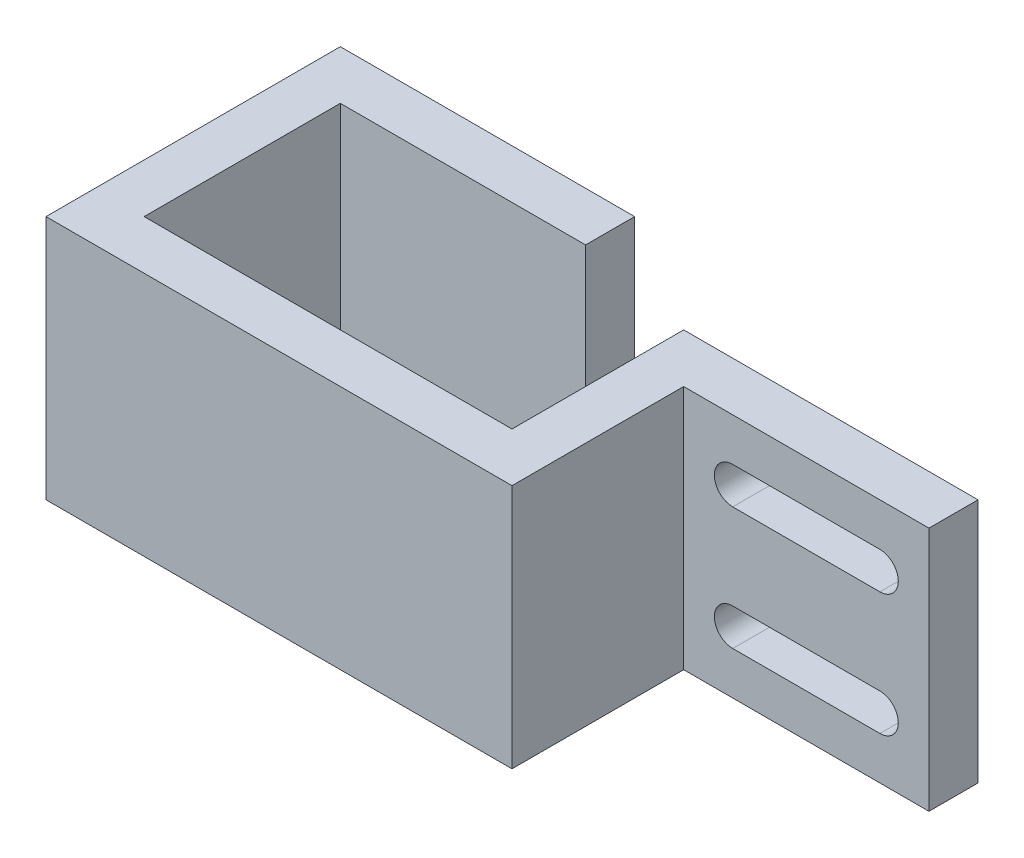
SolidWorks part; units mm, degrees
ref_plane "Front Plane" through (0, 0, 0) normal (0, 0, 1) x (1, 0, 0)
ref_plane "Top Plane" through (0, 0, 0) normal (0, 1, 0) x (1, 0, 0)
ref_plane "Right Plane" through (0, 0, 0) normal (1, 0, 0) x (0, 0, -1)
sketch "Croquis1" plane through (0, 0, 0) normal (0, 1, 0) x (1, 0, 0)
  line L0 (-19, 24) -> (-15, 24)
  line L1 (-15, 24) -> (-15, 4)
  line L2 (-15, 4) -> (15, 4)
  line L3 (15, 4) -> (15, 18)
  line L4 (15, 18) -> (39, 18)
  line L5 (39, 18) -> (39, 14)
  line L6 (39, 14) -> (19, 14)
  line L7 (19, 14) -> (19, 0)
  line L8 (19, 0) -> (-19, 0)
  line L9 (-19, 0) -> (-19, 24)
  point P2 (0, 0)
  dimension "D1" = 38
  dimension "D2" = 4
  dimension "D3" = 4
  dimension "D4" = 4
  dimension "D5" = 24
  dimension "D6" = 18
  dimension "D7" = 4
  dimension "D8" = 24
extrude "Saliente-Extruir1" add sketch "Croquis1" along normal blind 20
sketch "Croquis2" plane through (0, 0, -14) normal (0, 0, 1) x (1, 0, 0)
  line L0 (39, 10) -> (19, 10) construction
  line L1 (39, 20) -> (39, 0) construction
  line L2 (29, 20) -> (29, 10) construction
  line L3 (19, 20) -> (39, 20) construction
  line L4 (29, 15) -> (39, 15) construction
  line L5 (19, 20) -> (19, 0) construction
  line L6 (35, 16.5) -> (23, 16.5)
  line L7 (35, 13.5) -> (23, 13.5)
  line L8 (35, 3.5) -> (23, 3.5)
  line L9 (35, 6.5) -> (23, 6.5)
  arc A0 (35, 13.5) -> (35, 16.5) centre (35, 15) ccw
  arc A1 (23, 13.5) -> (23, 16.5) centre (23, 15) cw
  arc A2 (35, 6.5) -> (35, 3.5) centre (35, 5) cw
  arc A3 (23, 6.5) -> (23, 3.5) centre (23, 5) ccw
  point P15 (29, 13.5)
  point P20 (29, 16.5)
  dimension "D1" = 3
  dimension "D2" = 6
extrude "Cortar-Extruir1" cut sketch "Croquis2" against normal blind 20
sketch "Croquis3" plane through (-15, 0, 0) normal (1, 0, 0) x (0, 0, -1)
  line L0 (24, 20) -> (20, 20)
  line L1 (4, 20) -> (24, 20) construction
  line L2 (20, 20) -> (20, 0)
  line L3 (4, 0) -> (24, 0) construction
  line L4 (20, 0) -> (24, 0)
  line L5 (24, 0) -> (24, 20)
  dimension "D1" = 4
extrude "Saliente-Extruir2" add sketch "Croquis3" along normal blind 20
